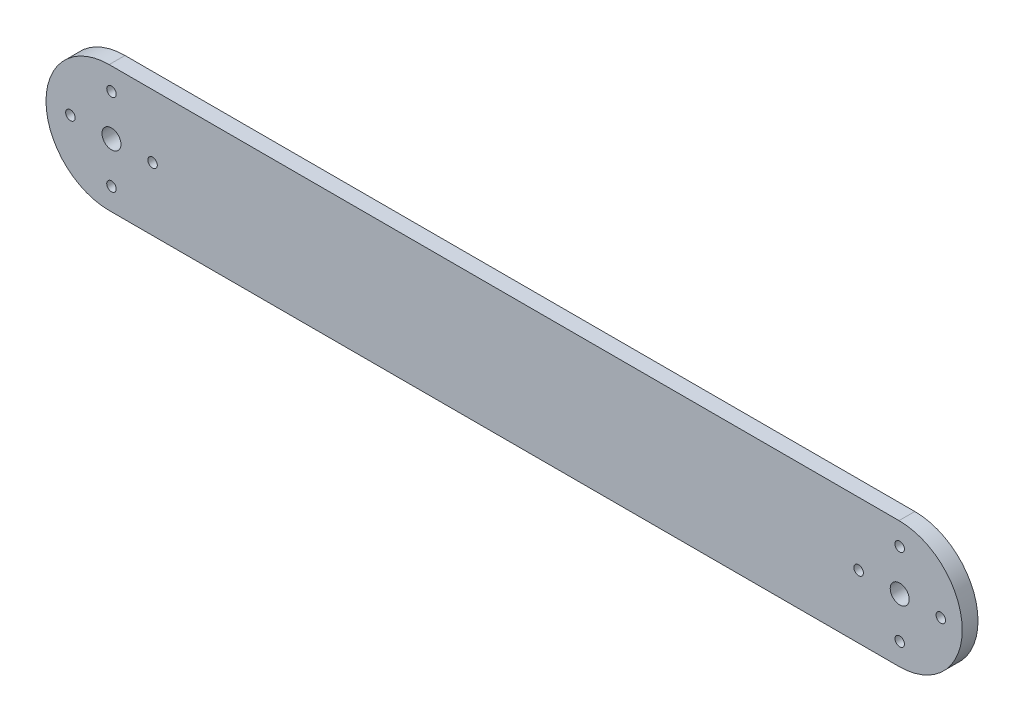
SolidWorks part; units mm, degrees
material "Epoxy, Unfilled"
ref_plane "Front Plane" through (0, 0, 0) normal (0, 0, 1) x (1, 0, 0)
ref_plane "Top Plane" through (0, 0, 0) normal (0, 1, 0) x (1, 0, 0)
ref_plane "Right Plane" through (0, 0, 0) normal (1, 0, 0) x (0, 0, -1)
sketch "Sketch1" plane through (0, 0, 0) normal (0, 0, 1) x (1, 0, 0)
  line L0 (125, 0) -> (-125, 0) construction
  line L1 (125, -20) -> (-125, -20)
  line L2 (125, 20) -> (-125, 20)
  arc A0 (125, -20) -> (125, 20) centre (125, 0) ccw
  arc A1 (-125, 20) -> (-125, -20) centre (-125, 0) ccw
  point P3 (0, 0)
  dimension "D2" = 20
  dimension "D1" = 250
extrude "Boss-Extrude1" add sketch "Sketch1" along normal blind 5
sketch "Sketch2" plane through (0, 0, 5) normal (0, 0, 1) x (1, 0, 0)
  arc A0 (-125, 20) -> (-125, -20) centre (-125, 0) ccw construction
  circle B0 centre (-124.275, 13) radius 1.5
  circle B1 centre (-111.275, 0) radius 1.5
  circle B2 centre (-124.275, -13) radius 1.5
  circle B3 centre (-137.275, 0) radius 1.5
  circle B4 centre (125.2163, 13) radius 1.5
  circle B5 centre (138.2163, 0) radius 1.5
  circle B6 centre (125.2163, -13) radius 1.5
  circle B7 centre (112.2163, 0) radius 1.5
sketch_block_instance "mounting connector-1"
sketch_block "mounting connector" parameters "D1"=3
sketch_block_instance "mounting connector-3"
extrude "Cut-Extrude1" cut sketch "Sketch2" against normal blind 5
sketch "Sketch3" plane through (0, 0, 0) normal (0, 0, -1) x (-1, 0, 0)
  circle A0 centre (-125.2163, 0) radius 3 construction
  circle A1 centre (-125.2163, 0) radius 3
extrude "Cut-Extrude2" cut sketch "Sketch3" against normal blind 5
sketch "Sketch4" plane through (0, 0, 0) normal (0, 0, -1) x (-1, 0, 0)
  circle A0 centre (124.275, 0) radius 3 construction
  circle A1 centre (124.275, 0) radius 3
extrude "Cut-Extrude3" cut sketch "Sketch4" against normal blind 10
